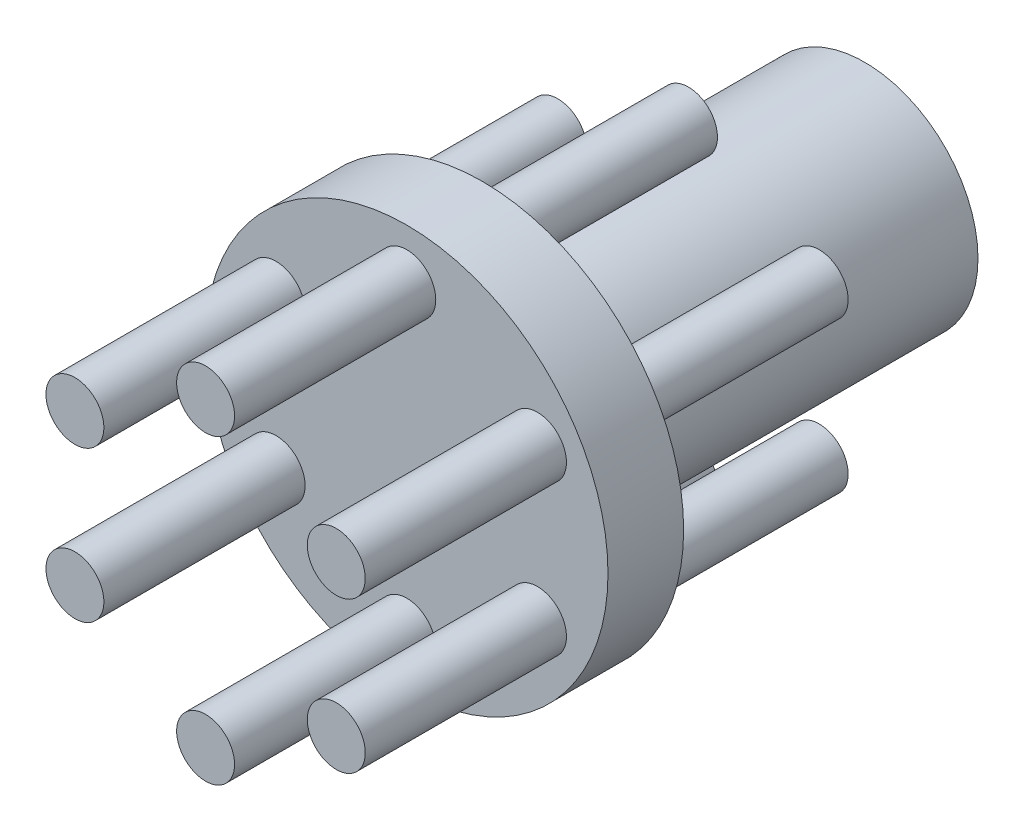
SolidWorks part; units mm, degrees
ref_plane "Front Plane" through (0, 0, 0) normal (0, 0, 1) x (1, 0, 0)
ref_plane "Top Plane" through (0, 0, 0) normal (0, 1, 0) x (1, 0, 0)
ref_plane "Right Plane" through (0, 0, 0) normal (1, 0, 0) x (0, 0, -1)
sketch "Sketch1" plane through (0, 0, 0) normal (0, 0, 1) x (1, 0, 0)
  circle A0 centre (0, 0) radius 12.7
  dimension "D1" = 25.4
extrude "Boss-Extrude1" add sketch "Sketch1" along normal blind 4.7752
sketch "Sketch2" plane through (0, 0, 0) normal (0, 0, -1) x (-1, 0, 0)
  circle A0 centre (0, 0) radius 7.1501
  dimension "D1" = 14.3002
extrude "Boss-Extrude2" add sketch "Sketch2" along normal blind 24.13
sketch "Sketch3" plane through (0, 0, 4.7752) normal (0, 0, 1) x (1, 0, 0)
  circle A0 centre (0, 0) radius 9.525 construction
  circle A1 centre (0, 9.525) radius 1.8288
  circle A2 centre (8.2489, 4.7625) radius 1.8288
  circle A3 centre (8.2489, -4.7625) radius 1.8288
  circle A4 centre (0, -9.525) radius 1.8288
  circle A5 centre (-8.2489, -4.7625) radius 1.8288
  circle A6 centre (-8.2489, 4.7625) radius 1.8288
  point P18 (0, 0)
  dimension "D1" = 19.05
  dimension "D2" = 3.6576
  dimension "D3" = 6
extrude "Boss-Extrude3" add sketch "Sketch3" along normal blind 12.7 and the other way blind 17.78
sketch "Sketch4" plane through (0, 0, 4.7752) normal (0, 0, 1) x (1, 0, 0)
  line L0 (0, 12.7) -> (0, -12.7) construction
  circle A0 centre (0, 0) radius 12.7 construction
